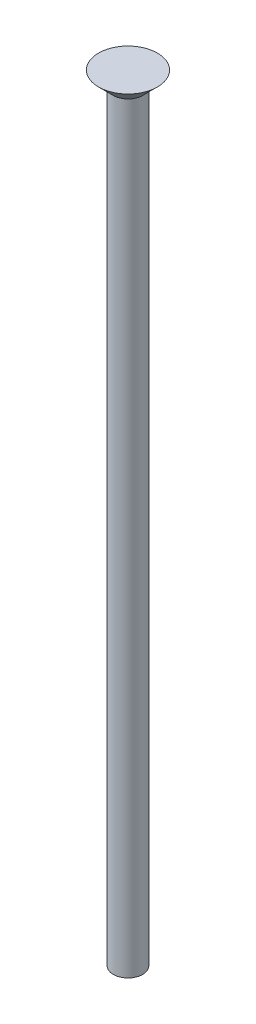
SolidWorks part; units mm, degrees
material "6061-T4 (SS)"
ref_plane "Front Plane" through (0, 0, 0) normal (0, 0, 1) x (1, 0, 0)
ref_plane "Top Plane" through (0, 0, 0) normal (0, 1, 0) x (1, 0, 0)
ref_plane "Right Plane" through (0, 0, 0) normal (1, 0, 0) x (0, 0, -1)
sketch "Sketch1" plane through (0, 0, 0) normal (0, 1, 0) x (1, 0, 0)
  circle A0 centre (0, 0) radius 1.6
  dimension "D1" = 3.2
extrude "Boss-Extrude1" add sketch "Sketch1" along normal up to surface (84.4 mm away)
sketch "Sketch3" plane through (0, 84.4, 0) normal (0, 1, 0) x (1, 0, 0)
  line L0 (-1.6, 0) -> (1.6, 0)
  circle A0 centre (0, 0) radius 1.6 construction
  circle A1 centre (0, 0) radius 1.6 construction
  point P6 (1.1874, 1.0724)
ref_plane "Plane2" through (0, 0, 0) normal (0, 0, 1) x (1, 0, 0)
sketch "Sketch4" plane through (0, 0, 0) normal (0, 0, 1) x (1, 0, 0)
  line L4 (1.6, 84.4) -> (1.6, 82.8)
  line L5 (1.6, 0) -> (1.6, 84.4) construction
  line L6 (1.6, 82.8) -> (3.2, 84.4)
  line L8 (3.2, 84.4) -> (1.6, 84.4)
  line L9 (-1.6, 84.4) -> (1.6, 84.4) construction
  line L10 (3.2, 84.4) -> (3.3, 84.4) construction
  line L11 (1.6, 82.7) -> (-0.8585, 82.7) construction
  line L12 (0, 84.4) -> (0, 82.7008) construction
  point P18 (0, 82.7008)
  dimension "D1" = 0.1
  dimension "D2" = 0.1
revolve "Revolve1" add sketch "Sketch4" angle 360 about L12
